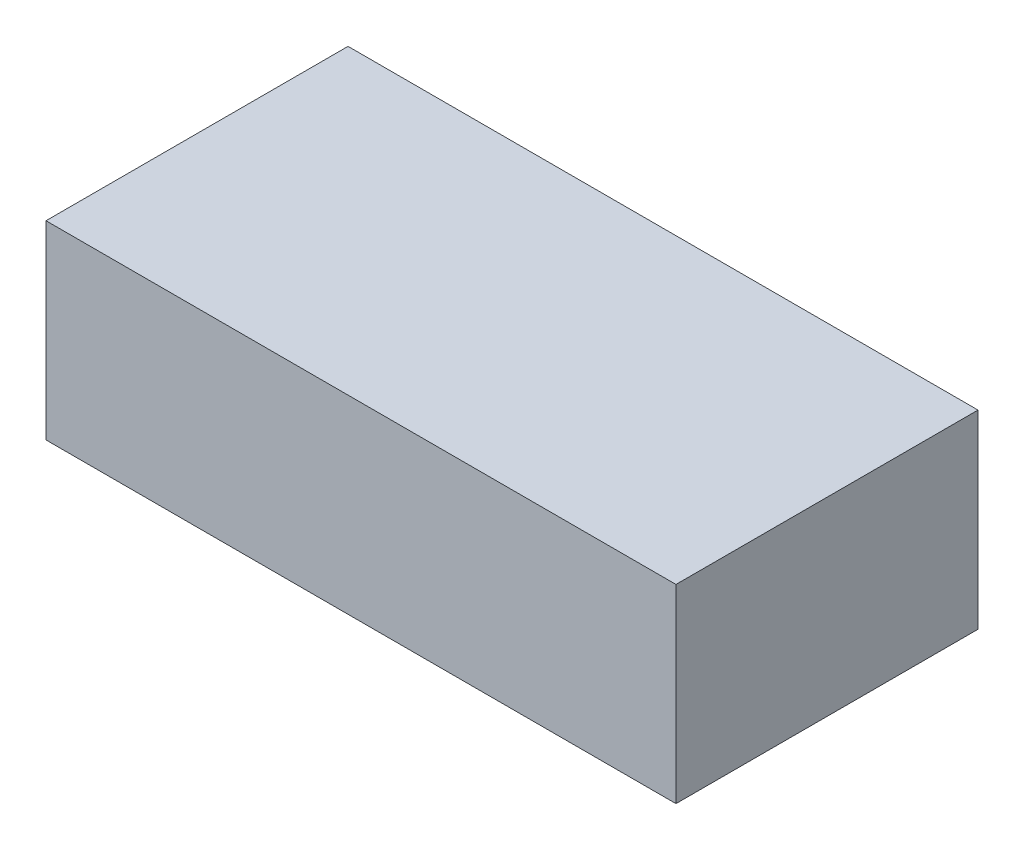
SolidWorks part; units mm, degrees
ref_plane "Front Plane" through (0, 0, 0) normal (0, 0, 1) x (1, 0, 0)
ref_plane "Top Plane" through (0, 0, 0) normal (0, 1, 0) x (1, 0, 0)
ref_plane "Right Plane" through (0, 0, 0) normal (1, 0, 0) x (0, 0, -1)
sketch "Sketch1" plane through (0, 0, 0) normal (0, 1, 0) x (1, 0, 0)
  line L1 (-36.5, 17.5) -> (36.5, 17.5)
  line L2 (-36.5, 17.5) -> (-36.5, -17.5)
  line L3 (-36.5, -17.5) -> (36.5, -17.5)
  line L4 (36.5, 17.5) -> (36.5, -17.5)
  point P5 (-36.5, 0)
  point P6 (0, 17.5)
  dimension "D1" = 35
  dimension "D2" = 73
extrude "Boss-Extrude1" add sketch "Sketch1" along normal blind 22
